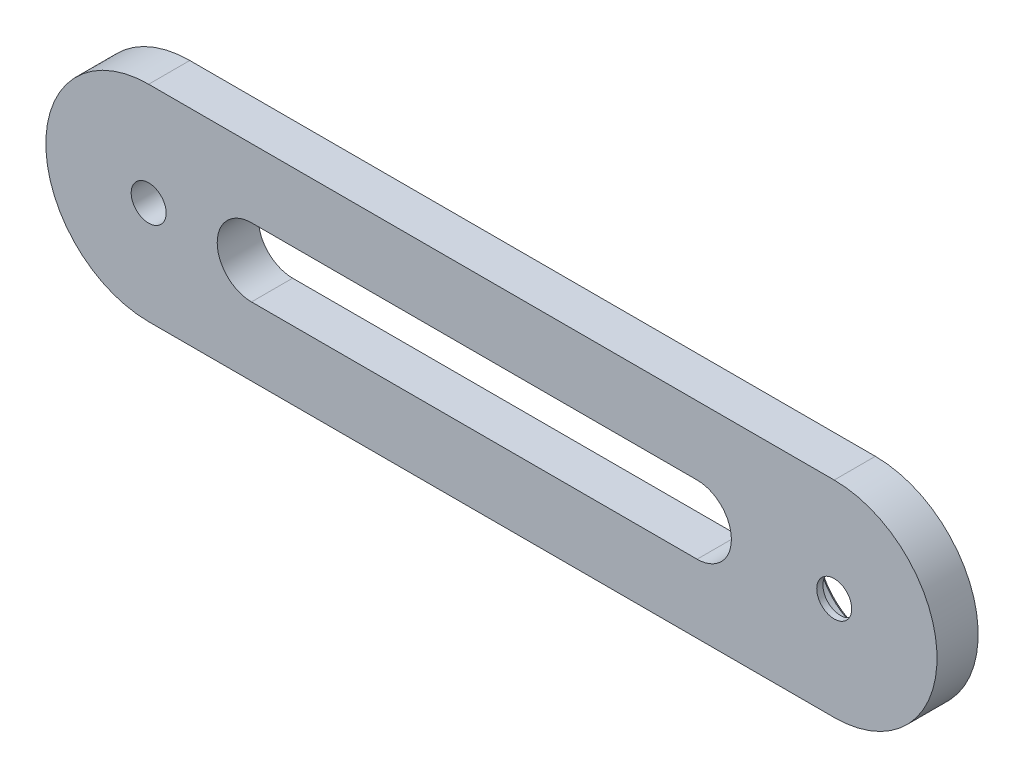
SolidWorks part; units mm, degrees
ref_plane "Front Plane" through (0, 0, 0) normal (0, 0, 1) x (1, 0, 0)
ref_plane "Top Plane" through (0, 0, 0) normal (0, 1, 0) x (1, 0, 0)
ref_plane "Right Plane" through (0, 0, 0) normal (1, 0, 0) x (0, 0, -1)
sketch "Sketch4" plane through (0, 0, 0) normal (0, 0, 1) x (1, 0, 0)
  line L0 (-50, 15) -> (50, 15)
  line L1 (50, -15) -> (-50, -15)
  line L2 (-50, 0) -> (50, 0) construction
  arc A0 (50, 15) -> (50, -15) centre (50, 0) cw
  arc A1 (-50, -15) -> (-50, 15) centre (-50, 0) cw
  dimension "D2" = 15
  dimension "D1" = 100
extrude "Boss-Extrude1" add sketch "Sketch4" along normal blind 6
sketch "Sketch9" plane through (0, 0, 0) normal (0, 0, -1) x (-1, 0, 0)
  circle A0 centre (-50, 0) radius 7.975
  dimension "D1" = 15.95
extrude "Cut-Extrude5" cut sketch "Sketch9" against normal blind 5.1
sketch "Sketch10" plane through (0, 0, 5.1) normal (0, 0, -1) x (-1, 0, 0)
  circle A0 centre (-50, 0) radius 2.55
  dimension "D1" = 5.1
extrude "Cut-Extrude6" cut sketch "Sketch10" against normal through all
sketch "Sketch11" plane through (0, 0, 0) normal (0, 0, -1) x (-1, 0, 0)
  circle A0 centre (50, 0) radius 2.55
  dimension "D1" = 5.1
extrude "Cut-Extrude7" cut sketch "Sketch11" against normal through all
chamfer "Chamfer1" distance 0.5 angle 45 1 edges at (42.025, 0, 0)
sketch "Sketch12" plane through (0, 0, 0) normal (0, 0, -1) x (-1, 0, 0)
  line L0 (-30, 5) -> (35, 5)
  line L1 (-30, -5) -> (35, -5)
  line L2 (-50, 15) -> (50, 15) construction
  line L3 (40, 0) -> (50, 0) construction
  line L4 (-50, 0) -> (-30, 0) construction
  arc A0 (-30, 5) -> (-30, -5) centre (-30, 0) ccw
  arc A1 (35, -5) -> (35, 5) centre (35, 0) ccw
  dimension "D3" = 20
  dimension "D1" = 10
  dimension "D2" = 10
extrude "Cut-Extrude8" cut sketch "Sketch12" against normal through all
